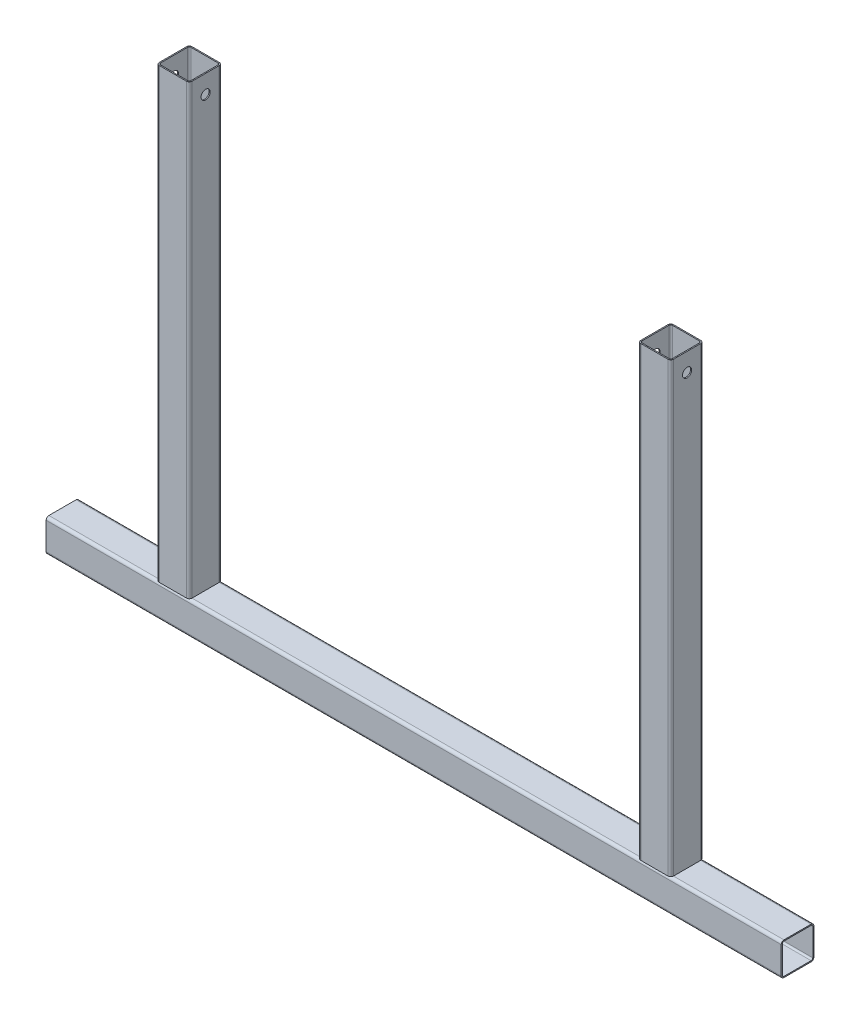
SolidWorks part; units mm, degrees
ref_plane "Front Plane" through (0, 0, 0) normal (0, 0, 1) x (1, 0, 0)
ref_plane "Top Plane" through (0, 0, 0) normal (0, 1, 0) x (1, 0, 0)
ref_plane "Right Plane" through (0, 0, 0) normal (1, 0, 0) x (0, 0, -1)
sketch "Sketch1" plane through (0, 0, 0) normal (0, 0, 1) x (1, 0, 0)
  line L0 (-400, 0) -> (400, 0)
  line L1 (-262, 0) -> (-262, 505)
  line L2 (-262, 505) -> (262, 505)
  line L3 (262, 0) -> (262, 505)
  line L4 (0, 0) -> (0, 606.9697) construction
  dimension "D1" = 800
  dimension "D2" = 524
  dimension "D3" = 505
other "Structural Member1"
ref_plane "Plane1" through (-400, 0, 0) normal (1, 0, 0) x (0, 1, 0)
sketch "Sketch11" plane through (-400, 0, 0) normal (1, 0, 0) x (0, 1, 0)
  line L1 (-14.8, -17.8) -> (14.8, -17.8)
  line L2 (-17.8, -14.8) -> (-17.8, 14.8)
  line L3 (-14.8, 17.8) -> (14.8, 17.8)
  line L4 (17.8, -14.8) -> (17.8, 14.8)
  line L5 (-17.8, -17.8) -> (17.8, 17.8) construction
  line L6 (-17.8, 17.8) -> (17.8, -17.8) construction
  line L7 (-14.8, 16.6) -> (14.8, 16.6)
  line L8 (-16.6, 14.8) -> (-16.6, -14.8)
  line L9 (-14.8, -16.6) -> (14.8, -16.6)
  line L10 (16.6, 14.8) -> (16.6, -14.8)
  line L11 (-16.6, 16.6) -> (16.6, -16.6) construction
  line L12 (-16.6, -16.6) -> (16.6, 16.6) construction
  arc A0 (14.8, 17.8) -> (17.8, 14.8) centre (14.8, 14.8) cw
  arc A1 (14.8, -17.8) -> (17.8, -14.8) centre (14.8, -14.8) ccw
  arc A2 (-14.8, -17.8) -> (-17.8, -14.8) centre (-14.8, -14.8) cw
  arc A3 (-17.8, 14.8) -> (-14.8, 17.8) centre (-14.8, 14.8) cw
  arc A4 (-16.6, -14.8) -> (-14.8, -16.6) centre (-14.8, -14.8) ccw
  arc A5 (14.8, -16.6) -> (16.6, -14.8) centre (14.8, -14.8) ccw
  arc A6 (14.8, 16.6) -> (16.6, 14.8) centre (14.8, 14.8) cw
  arc A7 (-14.8, 16.6) -> (-16.6, 14.8) centre (-14.8, 14.8) ccw
  point P0 (0, 0)
  point P5 (0, 0)
  point P35 (0, 0)
  dimension "D4" = 3
  dimension "D5" = 1.8
  dimension "D1" = 35.6
  dimension "D2" = 35.6
  dimension "D3" = 1.2
sketch "Sketch12" plane through (0, 0, 0) normal (1, 0, 0) x (0, 0, -1)
  line L0 (0, 0) -> (0, 606.9697) construction
  circle A0 centre (0, 485) radius 5
  dimension "D1" = 10
  dimension "D2" = 485
extrude "Cut-Extrude2" cut sketch "Sketch12" against normal through all and the other way through all
